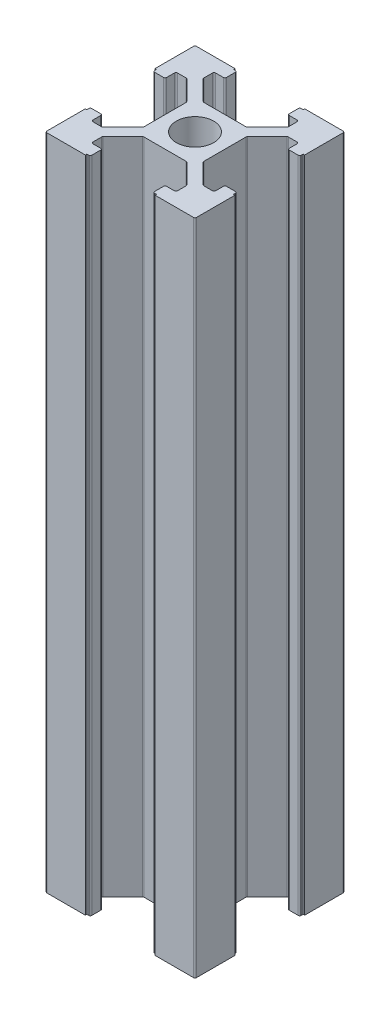
SolidWorks part; units mm, degrees
material "6063-O"
ref_plane "Ön Düzlem" through (0, 0, 0) normal (0, 0, 1) x (1, 0, 0)
ref_plane "Üst Düzlem" through (0, 0, 0) normal (0, 1, 0) x (1, 0, 0)
ref_plane "Sağ Düzlem" through (0, 0, 0) normal (1, 0, 0) x (0, 0, -1)
sketch "Sketch1" plane through (0, 0, 0) normal (0, 1, 0) x (1, 0, 0)
  line L0 (-10, 4.65) -> (-9.8, 4.65)
  line L1 (-9.8, -10) -> (-4.65, -10)
  line L2 (-10, -9.8) -> (-10, -4.65)
  line L3 (-9.8, 10) -> (-4.65, 10)
  line L4 (10, -9.8) -> (10, -4.65)
  line L5 (-10, -10) -> (10, 10) construction
  line L6 (-10, 10) -> (10, -10) construction
  line L7 (-9.8, 4.65) -> (-9.8, 4.4)
  line L8 (-9.6, 4.2) -> (-8.4, 4.2)
  line L9 (-4, 2.8172) -> (-4, -2.8172)
  line L10 (-8.2, 4.4) -> (-8.2, 5.45)
  line L11 (-8, 5.65) -> (-6.8328, 5.65)
  line L12 (-6.6914, 5.5914) -> (-4.0586, 2.9586)
  line L13 (-9.8, -4.65) -> (-10, -4.65)
  line L14 (-6.6914, -5.5914) -> (-4.0586, -2.9586)
  line L15 (-8, -5.65) -> (-6.8328, -5.65)
  line L16 (-8.2, -4.4) -> (-8.2, -5.45)
  line L17 (-9.6, -4.2) -> (-8.4, -4.2)
  line L18 (-9.8, -4.65) -> (-9.8, -4.4)
  line L19 (4.65, 10) -> (4.65, 9.8)
  line L20 (-10, 4.65) -> (-10, 9.8)
  line L21 (4.65, 9.8) -> (4.4, 9.8)
  line L22 (4.2, 9.6) -> (4.2, 8.4)
  line L23 (4.4, 8.2) -> (5.45, 8.2)
  line L24 (5.65, 8) -> (5.65, 6.8328)
  line L25 (5.5914, 6.6914) -> (2.9586, 4.0586)
  line L26 (2.8172, 4) -> (-2.8172, 4)
  line L27 (-5.5914, 6.6914) -> (-2.9586, 4.0586)
  line L28 (-5.65, 8) -> (-5.65, 6.8328)
  line L29 (-4.4, 8.2) -> (-5.45, 8.2)
  line L30 (-4.2, 9.6) -> (-4.2, 8.4)
  line L31 (-4.65, 9.8) -> (-4.4, 9.8)
  line L32 (-4.65, 9.8) -> (-4.65, 10)
  line L33 (10, -4.65) -> (9.8, -4.65)
  line L34 (9.8, -4.65) -> (9.8, -4.4)
  line L35 (9.6, -4.2) -> (8.4, -4.2)
  line L36 (8.2, -4.4) -> (8.2, -5.45)
  line L37 (8, -5.65) -> (6.8328, -5.65)
  line L38 (6.6914, -5.5914) -> (4.0586, -2.9586)
  line L39 (4, -2.8172) -> (4, 2.8172)
  line L40 (6.6914, 5.5914) -> (4.0586, 2.9586)
  line L41 (8, 5.65) -> (6.8328, 5.65)
  line L42 (8.2, 4.4) -> (8.2, 5.45)
  line L43 (9.6, 4.2) -> (8.4, 4.2)
  line L44 (9.8, 4.65) -> (9.8, 4.4)
  line L45 (9.8, 4.65) -> (10, 4.65)
  line L46 (-4.65, -10) -> (-4.65, -9.8)
  line L47 (-4.65, -9.8) -> (-4.4, -9.8)
  line L48 (-4.2, -9.6) -> (-4.2, -8.4)
  line L49 (-4.4, -8.2) -> (-5.45, -8.2)
  line L50 (-5.65, -8) -> (-5.65, -6.8328)
  line L51 (-5.5914, -6.6914) -> (-2.9586, -4.0586)
  line L52 (-2.8172, -4) -> (2.8172, -4)
  line L53 (5.5914, -6.6914) -> (2.9586, -4.0586)
  line L54 (5.65, -8) -> (5.65, -6.8328)
  line L55 (4.4, -8.2) -> (5.45, -8.2)
  line L56 (4.2, -9.6) -> (4.2, -8.4)
  line L57 (4.65, -9.8) -> (4.4, -9.8)
  line L58 (4.65, -9.8) -> (4.65, -10)
  line L59 (4.65, -10) -> (9.8, -10)
  line L60 (10, 4.65) -> (10, 9.8)
  line L61 (4.65, 10) -> (9.8, 10)
  arc A0 (-9.8, 4.4) -> (-9.6, 4.2) centre (-9.6, 4.4) ccw
  arc A1 (-9.8, -4.4) -> (-9.6, -4.2) centre (-9.6, -4.4) cw
  arc A2 (-8.4, 4.2) -> (-8.2, 4.4) centre (-8.4, 4.4) ccw
  arc A3 (-8.2, 5.45) -> (-8, 5.65) centre (-8, 5.45) cw
  arc A4 (-6.6914, 5.5914) -> (-6.8328, 5.65) centre (-6.8328, 5.45) ccw
  arc A5 (-4, 2.8172) -> (-4.0586, 2.9586) centre (-4.2, 2.8172) ccw
  arc A6 (-6.6914, -5.5914) -> (-6.8328, -5.65) centre (-6.8328, -5.45) cw
  arc A7 (-4, -2.8172) -> (-4.0586, -2.9586) centre (-4.2, -2.8172) cw
  arc A8 (-8, -5.65) -> (-8.2, -5.45) centre (-8, -5.45) cw
  arc A9 (-8.2, -4.4) -> (-8.4, -4.2) centre (-8.4, -4.4) ccw
  arc A10 (4.4, 9.8) -> (4.2, 9.6) centre (4.4, 9.6) ccw
  arc A11 (4.2, 8.4) -> (4.4, 8.2) centre (4.4, 8.4) ccw
  arc A12 (5.45, 8.2) -> (5.65, 8) centre (5.45, 8) cw
  arc A13 (5.5914, 6.6914) -> (5.65, 6.8328) centre (5.45, 6.8328) ccw
  arc A14 (2.8172, 4) -> (2.9586, 4.0586) centre (2.8172, 4.2) ccw
  arc A15 (-2.8172, 4) -> (-2.9586, 4.0586) centre (-2.8172, 4.2) cw
  arc A16 (-5.5914, 6.6914) -> (-5.65, 6.8328) centre (-5.45, 6.8328) cw
  arc A17 (-5.65, 8) -> (-5.45, 8.2) centre (-5.45, 8) cw
  arc A18 (-4.4, 8.2) -> (-4.2, 8.4) centre (-4.4, 8.4) ccw
  arc A19 (-4.4, 9.8) -> (-4.2, 9.6) centre (-4.4, 9.6) cw
  arc A20 (9.8, -4.4) -> (9.6, -4.2) centre (9.6, -4.4) ccw
  arc A21 (8.4, -4.2) -> (8.2, -4.4) centre (8.4, -4.4) ccw
  arc A22 (8.2, -5.45) -> (8, -5.65) centre (8, -5.45) cw
  arc A23 (6.6914, -5.5914) -> (6.8328, -5.65) centre (6.8328, -5.45) ccw
  arc A24 (4, -2.8172) -> (4.0586, -2.9586) centre (4.2, -2.8172) ccw
  arc A25 (4, 2.8172) -> (4.0586, 2.9586) centre (4.2, 2.8172) cw
  arc A26 (6.6914, 5.5914) -> (6.8328, 5.65) centre (6.8328, 5.45) cw
  arc A27 (8, 5.65) -> (8.2, 5.45) centre (8, 5.45) cw
  arc A28 (8.2, 4.4) -> (8.4, 4.2) centre (8.4, 4.4) ccw
  arc A29 (9.8, 4.4) -> (9.6, 4.2) centre (9.6, 4.4) cw
  arc A30 (-4.4, -9.8) -> (-4.2, -9.6) centre (-4.4, -9.6) ccw
  arc A31 (-4.2, -8.4) -> (-4.4, -8.2) centre (-4.4, -8.4) ccw
  arc A32 (-5.45, -8.2) -> (-5.65, -8) centre (-5.45, -8) cw
  arc A33 (-5.5914, -6.6914) -> (-5.65, -6.8328) centre (-5.45, -6.8328) ccw
  arc A34 (-2.8172, -4) -> (-2.9586, -4.0586) centre (-2.8172, -4.2) ccw
  arc A35 (2.8172, -4) -> (2.9586, -4.0586) centre (2.8172, -4.2) cw
  arc A36 (5.5914, -6.6914) -> (5.65, -6.8328) centre (5.45, -6.8328) cw
  arc A37 (5.65, -8) -> (5.45, -8.2) centre (5.45, -8) cw
  arc A38 (4.4, -8.2) -> (4.2, -8.4) centre (4.4, -8.4) ccw
  arc A39 (4.4, -9.8) -> (4.2, -9.6) centre (4.4, -9.6) cw
  arc A40 (-9.8, -10) -> (-10, -9.8) centre (-9.8, -9.8) cw
  arc A41 (9.8, -10) -> (10, -9.8) centre (9.8, -9.8) ccw
  arc A42 (10, 9.8) -> (9.8, 10) centre (9.8, 9.8) ccw
  arc A43 (-10, 9.8) -> (-9.8, 10) centre (-9.8, 9.8) cw
  circle A44 centre (0, 0) radius 2.5
  point P0 (0, 0)
  point P12 (-9.8, 4.2)
  point P27 (-9.8, -4.2)
  point P30 (-8.2, 4.2)
  point P33 (-8.2, 5.65)
  point P36 (-6.75, 5.65)
  point P39 (-4, 2.9)
  point P42 (-6.75, -5.65)
  point P45 (-4, -2.9)
  point P48 (-8.2, -5.65)
  point P51 (-8.2, -4.2)
  dimension "D11" = 0.2
  dimension "D13" = 0.2
  dimension "D14" = 5
  dimension "D1" = 20
  dimension "D2" = 20
  dimension "D3" = 5.35
  dimension "D4" = 0.2
  dimension "D5" = 0.45
  dimension "D6" = 1.6
  dimension "D7" = 4.2
  dimension "D8" = 1.45
  dimension "D9" = 1.45
  dimension "D10" = 135
  dimension "D12" = 4
extrude "Boss-Extrude1" add sketch "Sketch1" along normal blind 88
